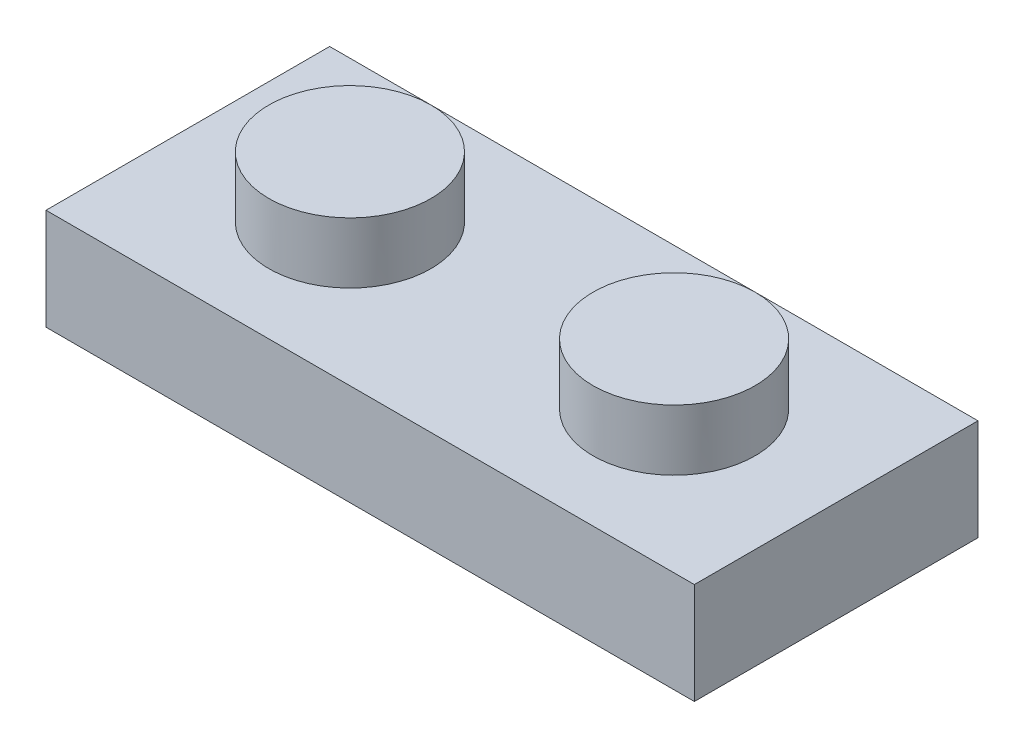
SolidWorks part; units mm, degrees
material "ABS"
ref_plane "Front Plane" through (0, 0, 0) normal (0, 0, 1) x (1, 0, 0)
ref_plane "Top Plane" through (0, 0, 0) normal (0, 1, 0) x (1, 0, 0)
ref_plane "Right Plane" through (0, 0, 0) normal (1, 0, 0) x (0, 0, -1)
sketch "Sketch1" plane through (0, 0, 0) normal (0, 0, 1) x (1, 0, 0)
  line L0 (-10.16, 0) -> (10.16, 0)
  line L1 (10.16, 0) -> (10.16, -3.175)
  line L2 (10.16, -3.175) -> (-10.16, -3.175)
  line L3 (-10.16, -3.175) -> (-10.16, 0)
  point P4 (0, -3.175)
  dimension "D1" = 20.32
  dimension "D2" = 3.175
extrude "Boss-Extrude2" add sketch "Sketch1" along normal mid plane 8.89
sketch "Sketch3" plane through (0, 0, 0) normal (0, 1, 0) x (1, 0, 0)
  line L0 (-10.16, 4.445) -> (0, -4.445) construction
  line L1 (10.16, -4.445) -> (-10.16, -4.445) construction
  line L2 (0, -4.445) -> (10.16, 4.445) construction
  circle A0 centre (-5.08, 0) radius 2.54
  circle A1 centre (5.08, 0) radius 2.54
  dimension "D1" = 5.08
  dimension "D2" = 5.08
extrude "Boss-Extrude3" add sketch "Sketch3" along normal blind 1.905
sketch "Sketch4" plane through (0, -3.175, 0) normal (0, -1, 0) x (1, 0, 0)
  line L0 (-8.89, 2.54) -> (-8.89, -2.54)
  line L1 (-8.89, -2.54) -> (8.89, -2.54)
  line L2 (8.89, -2.54) -> (8.89, 2.54)
  line L3 (8.89, 2.54) -> (-8.89, 2.54)
  line L5 (-10.16, 4.445) -> (-10.16, -4.445) construction
  line L6 (10.16, 4.445) -> (10.16, -4.445) construction
  line L7 (-10.16, -4.445) -> (0, 4.445) construction
  line L8 (-10.16, -4.445) -> (10.16, -4.445) construction
  line L9 (-10.16, 4.445) -> (10.16, 4.445) construction
  line L10 (0, 4.445) -> (10.16, -4.445) construction
  point P2 (-8.89, 0)
  dimension "D1" = 5.08
  dimension "D2" = 1.27
  dimension "D3" = 1.27
extrude "Cut-Extrude1" cut sketch "Sketch4" against normal blind 1.905
sketch "Sketch5" plane through (0, -1.27, 0) normal (0, -1, 0) x (1, 0, 0)
  line L0 (-10.16, -4.445) -> (0, 4.445) construction
  line L1 (-10.16, 4.445) -> (10.16, 4.445) construction
  line L2 (0, 4.445) -> (10.16, -4.445) construction
  circle A0 centre (-5.08, 0) radius 1.905
  circle A1 centre (5.08, 0) radius 1.905
  dimension "D1" = 3.81
  dimension "D2" = 3.81
extrude "Cut-Extrude2" cut sketch "Sketch5" against normal blind 2.54
sketch "Sketch6" plane through (0, -1.27, 0) normal (0, -1, 0) x (1, 0, 0)
  circle A0 centre (0, 0) radius 1.905
  circle A1 centre (0, 0) radius 0.9525
  dimension "D1" = 3.81
  dimension "D2" = 1.905
extrude "Boss-Extrude4" add sketch "Sketch6" along normal up to surface (1.905 mm away) up to face at (0, -3.175, 0)
